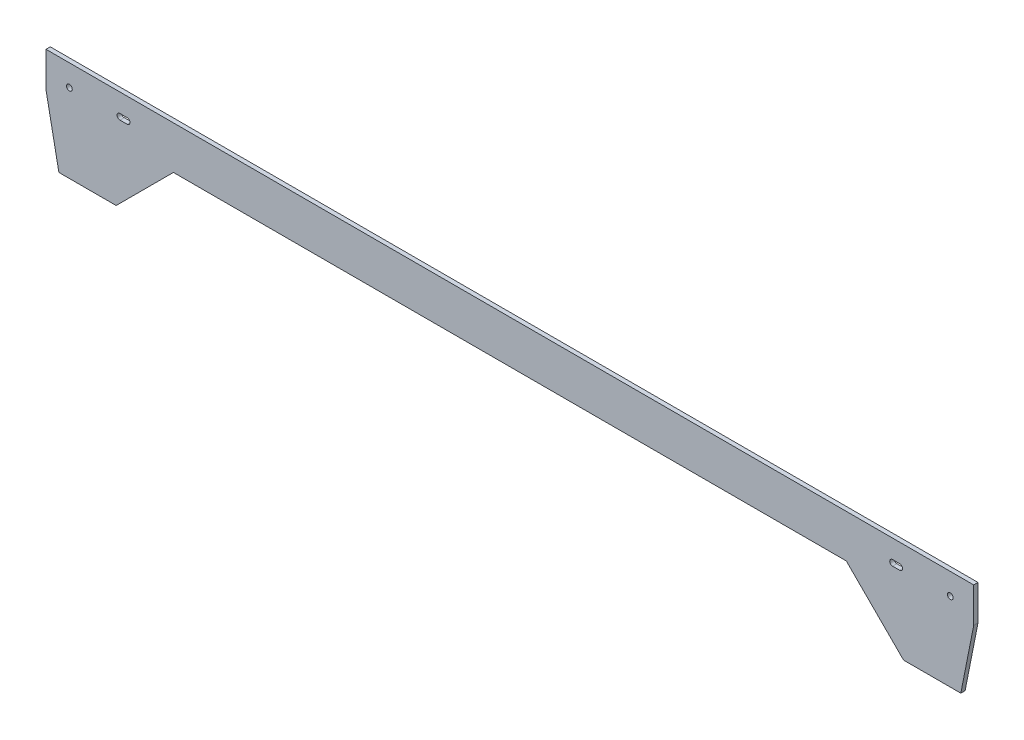
SolidWorks part; units mm, degrees
ref_plane "Alzado" through (0, 0, 0) normal (0, 0, 1) x (1, 0, 0)
ref_plane "Planta" through (0, 0, 0) normal (0, 1, 0) x (1, 0, 0)
ref_plane "Vista lateral" through (0, 0, 0) normal (1, 0, 0) x (0, 0, -1)
sketch "Croquis1" plane through (0, 0, 0) normal (0, 0, 1) x (1, 0, 0)
  line L0 (-600, -30) -> (-600, -110) construction
  line L1 (-600, -30) -> (-560, -30) construction
  line L2 (-600, -30) -> (-600, 30) construction
  line L3 (-600, 30) -> (600, 30)
  line L4 (600, -30) -> (600, 30) construction
  line L5 (-600, -30) -> (600, 30) construction
  line L6 (-600, 30) -> (600, -30) construction
  line L7 (600, -30) -> (560, -30) construction
  line L8 (600, -30) -> (600, 30) construction
  line L9 (600, 30) -> (560, 30)
  line L10 (560, -30) -> (560, 30) construction
  line L11 (-600, 30) -> (-560, 30)
  line L12 (-600, 30) -> (-600, -30) construction
  line L13 (-600, -30) -> (-560, -30) construction
  line L14 (-560, 30) -> (-560, -30) construction
  line L15 (-600, -110) -> (-550, -110)
  line L16 (-600, -110) -> (-630, -110)
  line L17 (-600, 0) -> (-638, 0) construction
  line L18 (-619, 0) -> (-619, 19) construction
  line L19 (-619, 0) -> (-619, -19) construction
  line L20 (-638, -19) -> (-600, -19) construction
  line L21 (-648, 30) -> (-648, -19)
  line L22 (-638, -19) -> (-638, 19) construction
  line L23 (-600, -19) -> (-600, 19)
  line L24 (-638, 19) -> (-600, 19) construction
  line L25 (-638, -19) -> (-600, 19) construction
  line L26 (-600, -19) -> (-638, 19) construction
  line L27 (-550, -110) -> (-470, -30)
  line L28 (-544.7, 4) -> (-534.7, 4)
  line L29 (-648, -19) -> (-630, -110)
  line L30 (550, -110) -> (470, -30)
  line L31 (-648, 30) -> (-600, 30)
  line L32 (-470, -30) -> (470, -30)
  line L33 (-560, -30) -> (-560, 30) construction
  line L34 (600, -110) -> (550, -110)
  line L35 (600, -110) -> (630, -110)
  line L36 (648, -19) -> (630, -110)
  line L37 (648, 30) -> (600, 30)
  line L38 (648, 30) -> (648, -19)
  line L39 (638, -19) -> (638, 19) construction
  line L40 (600, 0) -> (638, 0) construction
  line L41 (619, 0) -> (619, -19) construction
  line L42 (638, -19) -> (600, -19) construction
  line L43 (600, -19) -> (600, 19) construction
  line L44 (638, 19) -> (600, 19) construction
  line L45 (560, -30) -> (600, -30) construction
  line L46 (-600, 0) -> (-615.3, 0) construction
  line L47 (-580, -30) -> (-580, 30) construction
  line L48 (600, 30) -> (648, 30)
  line L49 (-544.7, -4) -> (-534.1852, -4)
  line L50 (0, 0) -> (0, -30) construction
  line L51 (544.7, -4) -> (534.1852, -4)
  line L52 (544.7, 4) -> (534.7, 4)
  circle A0 centre (-615.3, 0) radius 4
  arc A1 (-544.7, -4) -> (-544.7, 4) centre (-544.7, 0) cw
  arc A2 (544.7, -4) -> (544.7, 4) centre (544.7, 0) ccw
  circle A3 centre (615.3, 0) radius 4
  arc A4 (-534.7, -4) -> (-534.7, 4) centre (-534.7, 0) ccw
  arc A5 (544.7, -4) -> (544.7, 4) centre (544.7, 0) ccw
  arc A6 (534.7, -4) -> (534.7, 4) centre (534.7, 0) cw
  point P0 (0, 0)
  dimension "D14" = 8
  dimension "D16" = 8
  dimension "D17" = 10
  dimension "D1" = 1200
  dimension "D2" = 60
  dimension "D3" = 40
  dimension "D4" = 40
  dimension "D5" = 50
  dimension "D6" = 30
  dimension "D7" = 38
  dimension "D8" = 38
  dimension "D9" = 135
  dimension "D10" = 49
  dimension "D11" = 113.1371
  dimension "D12" = 92.7631
  dimension "D13" = 15.3
extrude "Saliente-Extruir1" add sketch "Croquis1" along normal blind 6
